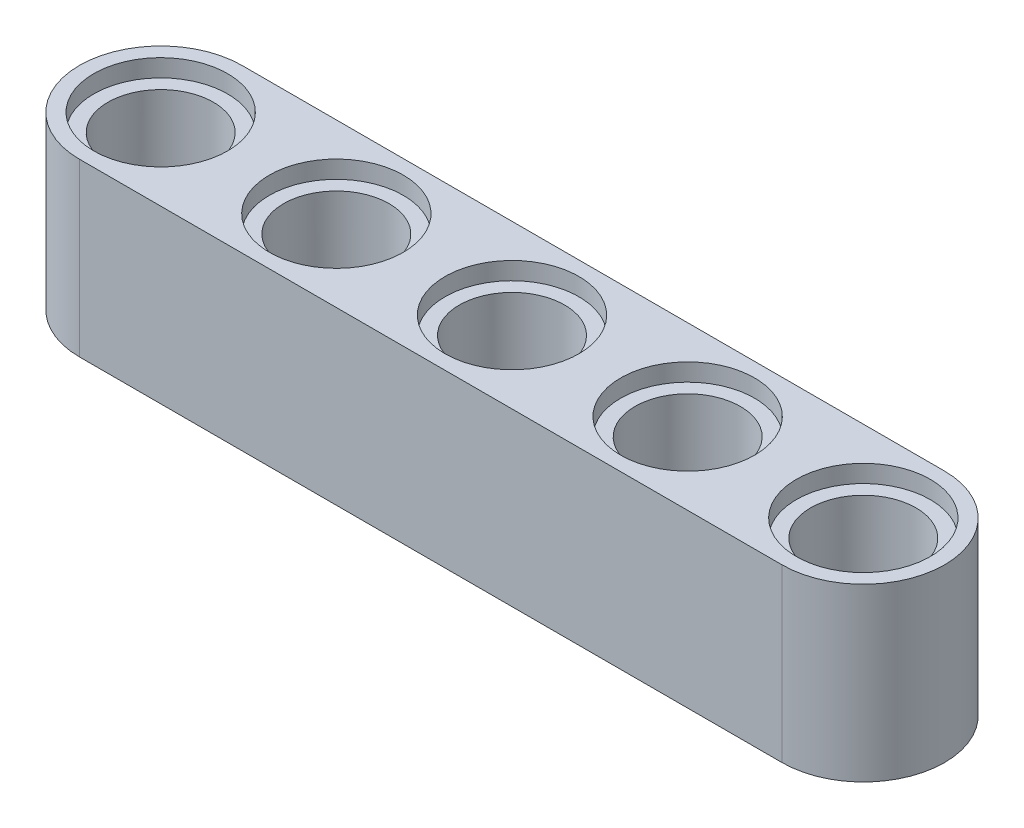
SolidWorks part; units mm, degrees
ref_plane "Front Plane" through (0, 0, 0) normal (0, 0, 1) x (1, 0, 0)
ref_plane "Top Plane" through (0, 0, 0) normal (0, 1, 0) x (1, 0, 0)
ref_plane "Right Plane" through (0, 0, 0) normal (1, 0, 0) x (0, 0, -1)
sketch "Sketch1" plane through (0, 0, 0) normal (0, 1, 0) x (1, 0, 0)
  line L1 (-16, 3.7) -> (16, 3.7)
  line L2 (0, -3.7) -> (16, -3.7)
  line L4 (0, -3.7) -> (-16, -3.7)
  arc A9 (16, 3.7) -> (16, -3.7) centre (16, 0) cw
  arc A10 (-16, 3.7) -> (-16, -3.7) centre (-16, 0) ccw
  point P20 (8, -3.7)
  point P25 (-8, -3.7)
  dimension "D1" = 3.7
  dimension "D5" = 3.7
  dimension "D2" = 32
extrude "Boss-Extrude3" add sketch "Sketch1" along normal blind 7.8 contours L4 A10 L1 A9 L2
sketch "Sketch2" plane through (0, 7.8, 0) normal (0, 1, 0) x (1, 0, 0)
  circle A0 centre (0, 0) radius 2.4
  circle A2 centre (8, 0) radius 2.4
  circle A5 centre (16, 0) radius 2.4
  circle A6 centre (-16, 0) radius 2.4
  circle A9 centre (-8, 0) radius 2.4
  dimension "D1" = 4.8
  dimension "D2" = 8
extrude "Cut-Extrude6" cut sketch "Sketch2" against normal blind 7.8 contours A6 | A9 | A0 | A2 | A5
sketch "Sketch3" plane through (0, 7.8, 0) normal (0, 1, 0) x (1, 0, 0)
  circle A0 centre (0, 0) radius 3.05
  circle A1 centre (8, 0) radius 3.05
  circle A2 centre (16, 0) radius 3.05
  circle A3 centre (-16, 0) radius 3.05
  circle A4 centre (-8, 0) radius 3.05
  dimension "D1" = 6.1
  dimension "D2" = 8
extrude "Cut-Extrude7" cut sketch "Sketch3" against normal blind 0.8
sketch "Sketch4" plane through (0, 0, 0) normal (0, -1, 0) x (1, 0, 0)
  circle A0 centre (0, 0) radius 3.05
  circle A1 centre (8, 0) radius 3.05
  circle A2 centre (16, 0) radius 3.05
  circle A3 centre (-16, 0) radius 3.05
  circle A4 centre (-8, 0) radius 3.05
  dimension "D1" = 6.1
  dimension "D2" = 8
extrude "Cut-Extrude8" cut sketch "Sketch4" against normal blind 0.8
